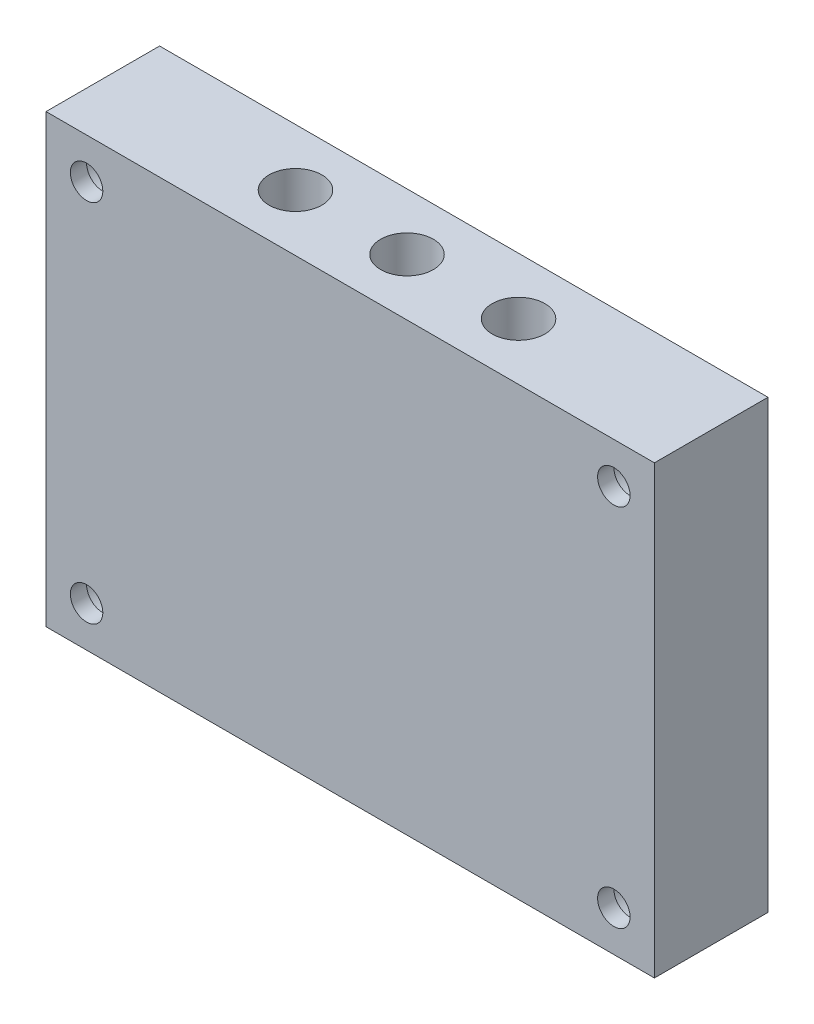
SolidWorks part; units mm, degrees
ref_plane "Front Plane" through (0, 0, 0) normal (0, 0, 1) x (1, 0, 0)
ref_plane "Top Plane" through (0, 0, 0) normal (0, 1, 0) x (1, 0, 0)
ref_plane "Right Plane" through (0, 0, 0) normal (1, 0, 0) x (0, 0, -1)
sketch "Sketch2" plane through (0, 0, 0) normal (0, 0, 1) x (1, 0, 0)
  line L1 (0, 0) -> (-75, 0)
  line L2 (0, 0) -> (0, -55)
  line L3 (0, -55) -> (-75, -55)
  line L4 (-75, 0) -> (-75, -55)
  line L5 (-65, -10) -> (-10, -10)
  line L6 (-65, -10) -> (-65, -45)
  line L7 (-65, -45) -> (-10, -45)
  line L8 (-10, -10) -> (-10, -45)
  dimension "D1" = 55
  dimension "D2" = 35
  dimension "D3" = 10
  dimension "D4" = 10
  dimension "D5" = 10
  dimension "D6" = 10
extrude "Boss-Extrude1" add sketch "Sketch2" along normal blind 12
sketch "Sketch3" plane through (0, 0, 12) normal (0, 0, 1) x (1, 0, 0)
  line L1 (-75, 0) -> (0, 0)
  line L2 (-75, 0) -> (-75, -55)
  line L3 (-75, -55) -> (0, -55)
  line L4 (0, 0) -> (0, -55)
extrude "Boss-Extrude2" add sketch "Sketch3" along normal blind 2
sketch "Sketch5" plane through (0, -45, 0) normal (0, 1, 0) x (1, 0, 0)
  line L0 (-56.5717, -12) -> (-56.5717, -2) construction
  line L1 (-65, -12) -> (-65, -6)
  line L2 (-65, -12) -> (-10, -12) construction
  line L7 (-56.5717, -7) -> (-10, -7) construction
  line L8 (-10, -12) -> (-10, 0) construction
  circle A0 centre (-51.25, -7) radius 1.32
  circle A1 centre (-37.5, -7) radius 1.32
  circle A2 centre (-23.75, -7) radius 1.32
  dimension "D1" = 10
  dimension "D2" = 2.64
  dimension "D3" = 13.75
  dimension "D5" = 13.75
  dimension "D4" = 3
extrude "Cut-Extrude1" cut sketch "Sketch5" against normal through all and the other way through all contours A0 | A2 | A1
sketch "Sketch6" plane through (0, 0, 0) normal (0, 1, 0) x (1, 0, 0)
  circle A0 centre (-51.25, -7) radius 3.25
  circle A1 centre (-37.5, -7) radius 3.25
  circle A2 centre (-23.75, -7) radius 3.25
  dimension "D1" = 6.5
  dimension "D3" = 13.75
  dimension "D2" = 3
extrude "Cut-Extrude2" cut sketch "Sketch6" against normal blind 8
sketch "Sketch7" plane through (0, 0, 14) normal (0, 0, 1) x (1, 0, 0)
  line L0 (-65, -10) -> (-10, -45) construction
  line L1 (-53.375, -11.625) -> (-21.625, -11.625) construction
  line L2 (-10, -10) -> (-65, -45) construction
  line L3 (-37.5, -27.5) -> (-37.5, -18.812) construction
  line L4 (-21.625, -11.625) -> (-21.625, -43.375) construction
  line L5 (-21.625, -43.375) -> (-53.375, -43.375) construction
  line L6 (-53.375, -43.375) -> (-53.375, -11.625) construction
  line L7 (-53.375, -11.625) -> (-21.625, -43.375) construction
  line L8 (-53.375, -43.375) -> (-21.625, -11.625) construction
  line L9 (-37.5, -27.5) -> (-29.3223, -27.5) construction
  circle A0 centre (-53.375, -11.625) radius 2
  circle A1 centre (-21.625, -11.625) radius 2
  circle A2 centre (-21.625, -43.375) radius 2
  circle A3 centre (-53.375, -43.375) radius 2
  dimension "D1" = 4
  dimension "D4" = 31.75
  dimension "D2" = 2
  dimension "D3" = 2
extrude "Cut-Extrude3" [suppressed] cut sketch "Sketch7" against normal through all contours A1 | A0 | A3 | A2
sketch "Sketch8" plane through (0, 0, 0) normal (0, 0, -1) x (-1, 0, 0)
  line L0 (0, 0) -> (75, -55) construction
  line L1 (37.5, -27.5) -> (41.2226, -22.4238) construction
  line L2 (0, -55) -> (75, 0) construction
  line L3 (0, 0) -> (10, -10) construction
  line L4 (65, -10) -> (75, 0) construction
  line L5 (65, -45) -> (75, -55) construction
  line L6 (5, -5) -> (70, -5) construction
  line L7 (10, -45) -> (0, -55) construction
  line L8 (70, -5) -> (70, -50) construction
  line L9 (70, -50) -> (5, -50) construction
  line L10 (5, -50) -> (5, -5) construction
  circle A0 centre (5, -5) radius 3.25
  circle A1 centre (70, -5) radius 3.25
  circle A2 centre (70, -50) radius 3.25
  circle A3 centre (5, -50) radius 3.25
  dimension "D1" = 6.5
  dimension "D3" = 2
  dimension "D4" = 2
extrude "Cut-Extrude4" cut sketch "Sketch8" against normal blind 12
sketch "Sketch9" plane through (0, 0, 0) normal (0, 0, -1) x (-1, 0, 0)
  circle A0 centre (5, -5) radius 2
  circle A5 centre (70, -5) radius 2
  circle A6 centre (70, -50) radius 2
  circle A7 centre (5, -50) radius 2
  dimension "D1" = 4
  dimension "D2" = 2
  dimension "D3" = 2
extrude "Cut-Extrude5" cut sketch "Sketch9" against normal through all
equation "\"A\"=10"
equation "\"D3@Sketch2\"=\"A\""
equation "\"D4@Sketch2\"=\"A\""
equation "\"D5@Sketch2\"=\"A\""
equation "\"D6@Sketch2\"=\"A\""
